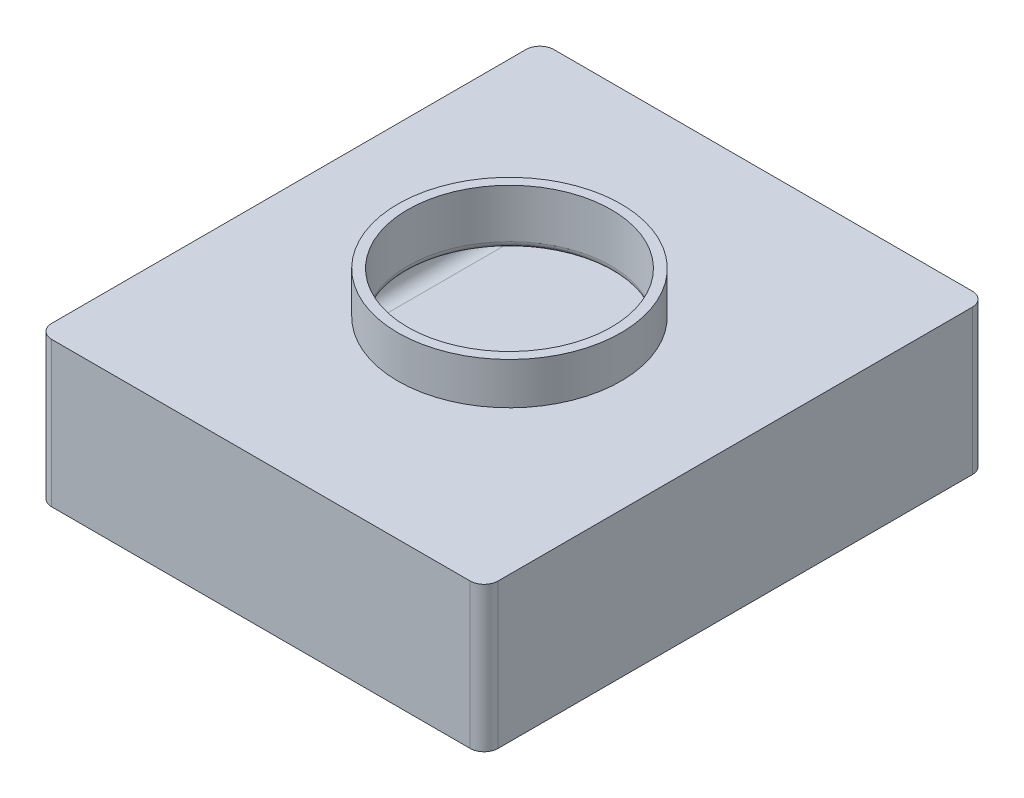
SolidWorks part; units mm, degrees
material "PE Low Density Film"
ref_plane "Front Plane" through (0, 0, 0) normal (0, 0, 1) x (1, 0, 0)
ref_plane "Top Plane" through (0, 0, 0) normal (0, 1, 0) x (1, 0, 0)
ref_plane "Right Plane" through (0, 0, 0) normal (1, 0, 0) x (0, 0, -1)
sketch "Sketch1" plane through (0, 0, 0) normal (0, 1, 0) x (1, 0, 0)
  line L1 (-149.7128, 123.8029) -> (40.7872, 123.8029)
  line L2 (-149.7128, 123.8029) -> (-149.7128, -92.0971)
  line L3 (-149.7128, -92.0971) -> (40.7872, -92.0971)
  line L4 (40.7872, 123.8029) -> (40.7872, -92.0971)
  line L5 (-156.0628, 130.1529) -> (47.1372, 130.1529)
  line L6 (-156.0628, 130.1529) -> (-156.0628, -98.4471)
  line L7 (-156.0628, -98.4471) -> (47.1372, -98.4471)
  line L8 (47.1372, 130.1529) -> (47.1372, -98.4471)
  dimension "D1" = 215.9
  dimension "D2" = 190.5
  dimension "D3" = 6.35
  dimension "D4" = 6.35
  dimension "D5" = 6.35
  dimension "D6" = 6.35
extrude "Boss-Extrude1" add sketch "Sketch1" along normal blind 53.34
sketch "Sketch2" plane through (0, 0, 0) normal (0, -1, 0) x (-1, 0, 0)
  line L1 (-47.1372, 130.1529) -> (156.0628, 130.1529)
  line L2 (-47.1372, 130.1529) -> (-47.1372, -98.4471)
  line L3 (-47.1372, -98.4471) -> (156.0628, -98.4471)
  line L4 (156.0628, 130.1529) -> (156.0628, -98.4471)
extrude "Boss-Extrude2" add sketch "Sketch2" along normal blind 6.35
sketch "Sketch3" plane through (0, 53.34, 0) normal (0, 1, 0) x (1, 0, 0)
  line L1 (-156.0628, 130.1529) -> (47.1372, 130.1529)
  line L2 (-156.0628, 130.1529) -> (-156.0628, -98.4471)
  line L3 (-156.0628, -98.4471) -> (47.1372, -98.4471)
  line L4 (47.1372, 130.1529) -> (47.1372, -98.4471)
extrude "Boss-Extrude3" add sketch "Sketch3" along normal blind 6.35
sketch "Sketch5" plane through (0, 59.69, 0) normal (0, 1, 0) x (1, 0, 0)
  circle A0 centre (-54.4628, 14.7061) radius 46.355
  dimension "D1" = 92.71
extrude "Cut-Extrude1" cut sketch "Sketch5" against normal up to next
fillet "Fillet5" radius 6.35 16 edges at (47.1372, 26.67, 98.4471) (-156.0628, 26.67, 98.4471) (-156.0628, 26.67, -130.1529) (47.1372, 26.67, -130.1529) (-54.4628, 53.34, 92.0971) (40.7872, 26.67, 92.0971) (40.7872, 53.34, -15.8529) (40.7872, 26.67, -123.8029) (-54.4628, 53.34, -123.8029) (-54.4628, 0, -123.8029) (-149.7128, 53.34, -15.8529) (-149.7128, 0, -15.8529) (-54.4628, 0, 92.0971) (40.7872, 0, -15.8529) (-149.7128, 26.67, 92.0971) (-149.7128, 26.67, -123.8029)
sketch "Sketch6" plane through (0, 59.69, 0) normal (0, 1, 0) x (1, 0, 0)
  circle A0 centre (-54.4628, 14.7061) radius 50.8
  circle A1 centre (-54.4628, 14.7061) radius 46.355
  dimension "4 in" = 101.6
extrude "Boss-Extrude4" add sketch "Sketch6" along normal blind 19.05
fillet "Fillet6" radius 3.175 1 edges at (-54.4628, 53.34, 31.6489)
